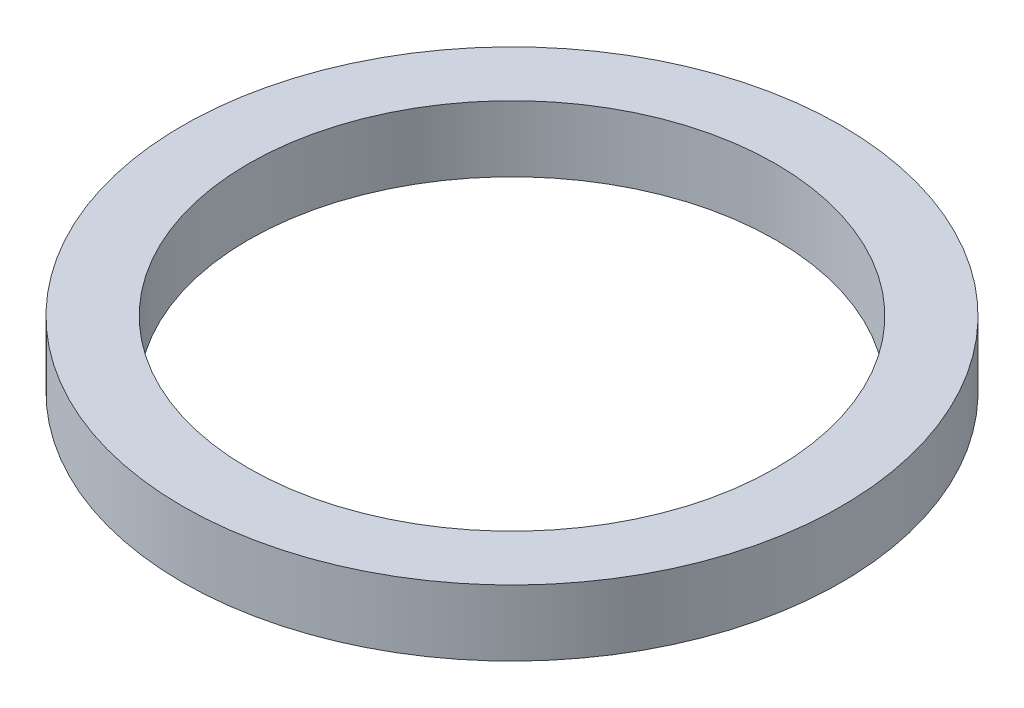
SolidWorks part; units mm, degrees
ref_plane "前视基准面" through (0, 0, 0) normal (0, 0, 1) x (1, 0, 0)
ref_plane "上视基准面" through (0, 0, 0) normal (0, 1, 0) x (1, 0, 0)
ref_plane "右视基准面" through (0, 0, 0) normal (1, 0, 0) x (0, 0, -1)
sketch "草图2" plane through (0, 0, 0) normal (0, 1, 0) x (1, 0, 0)
  circle A0 centre (0, 0) radius 50
  dimension "D1" = 100
extrude "凸台-拉伸1" add sketch "草图2" along normal blind 10
sketch "草图3" plane through (0, 10, 0) normal (0, 1, 0) x (1, 0, 0)
  circle A0 centre (0, 0) radius 40
  dimension "D1" = 80
extrude "切除-拉伸1" cut sketch "草图3" against normal blind 20
